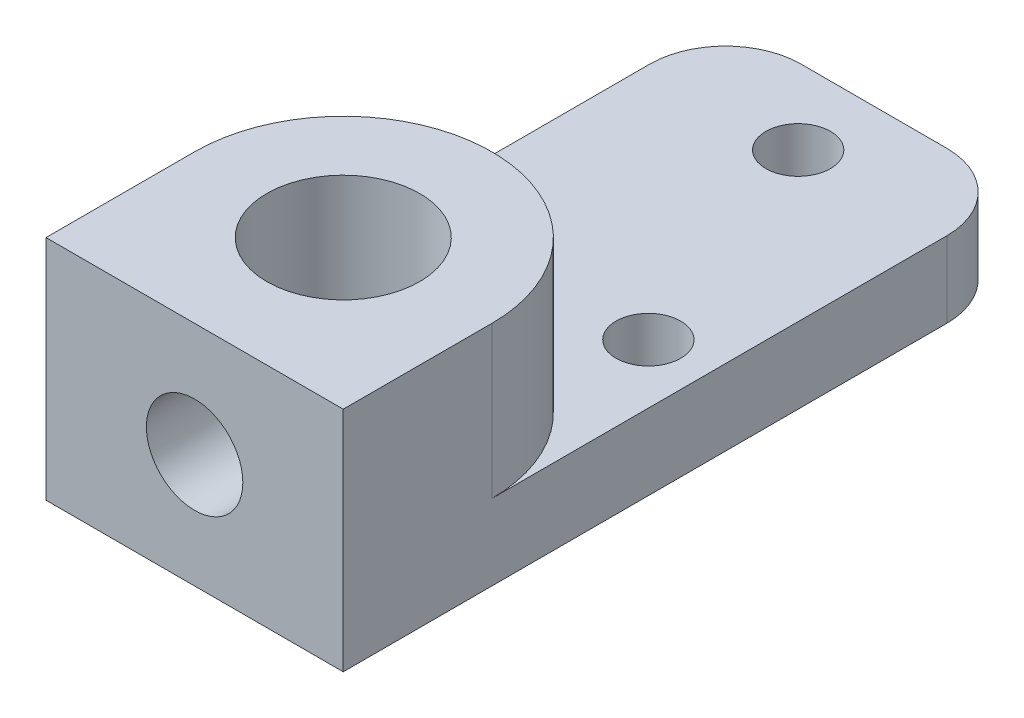
SolidWorks part; units mm, degrees
ref_plane "前视基准面" through (0, 0, 0) normal (0, 0, 1) x (1, 0, 0)
ref_plane "上视基准面" through (0, 0, 0) normal (0, 1, 0) x (1, 0, 0)
ref_plane "右视基准面" through (0, 0, 0) normal (1, 0, 0) x (0, 0, -1)
ref_plane "基准面4" through (0, 36.5125, 0) normal (0, 1, 0) x (1, 0, 0)
sketch "草图1" plane through (0, 36.5125, 0) normal (0, 1, 0) x (1, 0, 0)
  line L0 (6.223, -6.223) -> (6.223, 22.225)
  line L1 (6.223, 22.225) -> (-6.223, 22.225)
  line L2 (-6.223, 22.225) -> (-6.223, -6.223)
  line L3 (-6.223, -6.223) -> (6.223, -6.223)
extrude "凸台-拉伸1" add sketch "草图1" against normal blind 9.525
sketch "草图2" plane through (0, 36.5125, 0) normal (0, 1, 0) x (-1, 0, 0)
  line L0 (6.223, -22.225) -> (6.223, 0)
  line L1 (-6.223, 0) -> (-6.223, -22.225)
  line L2 (-6.223, -22.225) -> (6.223, -22.225)
  arc A0 (6.223, 0) -> (-6.223, 0) centre (0, 0) cw
extrude "切除-拉伸1" cut sketch "草图2" against normal blind 6.35
hole_wizard "M2.5 间隙孔1" positions "草图4" profile "草图3" hole size "M2.5" standard "ANSI Metric"
sketch "草图4" plane through (0, 26.9875, 0) normal (0, -1, 0) x (-1, 0, 0)
  point P0 (-3.7423, 9.0346)
  point P1 (3.7423, 9.0346)
  point P2 (0, 19.05)
sketch "草图3" plane through (3.7423, 26.9875, -9.0346) normal (1, 0, 0) x (0, 0, -1)
  line L0 (0, 0) -> (0, 9.525)
  line L1 (0, 9.525) -> (1.3525, 9.525)
  line L2 (1.3525, 9.525) -> (1.3525, 0)
  line L5 (1.3525, 0) -> (0, 0)
  line L11 (0, -6.35) -> (0, 107.95) construction
  dimension "通孔孔直径" = 2.7051
  dimension "通孔孔深度" = 9.525
hole_wizard "M6 间隙孔1" positions "草图6" profile "草图5" hole size "M6" standard "ANSI Metric"
sketch "草图6" plane through (0, 36.5125, 0) normal (0, 1, 0) x (1, 0, 0)
  point P0 (0, 0)
sketch "草图5" plane through (0, 36.5125, 0) normal (1, 0, 0) x (0, 0, 1)
  line L0 (0, 0) -> (0, 9.525)
  line L1 (0, 9.525) -> (3.2004, 9.525)
  line L2 (3.2004, 9.525) -> (3.2004, 0)
  line L5 (3.2004, 0) -> (0, 0)
  line L11 (0, -6.35) -> (0, 107.95) construction
  dimension "通孔孔直径" = 6.4008
  dimension "通孔孔深度" = 9.525
hole_wizard "M3.5 间隙孔1" positions "草图8" profile "草图7" hole size "M3.5" standard "ANSI Metric"
sketch "草图8" plane through (0, 0, 6.223) normal (0, 0, 1) x (1, 0, 0)
  point P0 (0, 31.75)
sketch "草图7" plane through (0, 31.75, 6.223) normal (1, 0, 0) x (0, -1, 0)
  line L0 (0, 0) -> (0, 3.0226)
  line L1 (0, 3.0226) -> (2.0193, 3.0226)
  line L2 (2.0193, 3.0226) -> (2.0193, 0)
  line L5 (2.0193, 0) -> (0, 0)
  line L11 (0, -6.35) -> (0, 107.95) construction
  dimension "通孔孔直径" = 4.0386
  dimension "通孔孔深度" = 3.0226
fillet "圆角1" radius 3.175 2 edges at (6.223, 28.575, -22.225) (-6.223, 28.575, -22.225)
